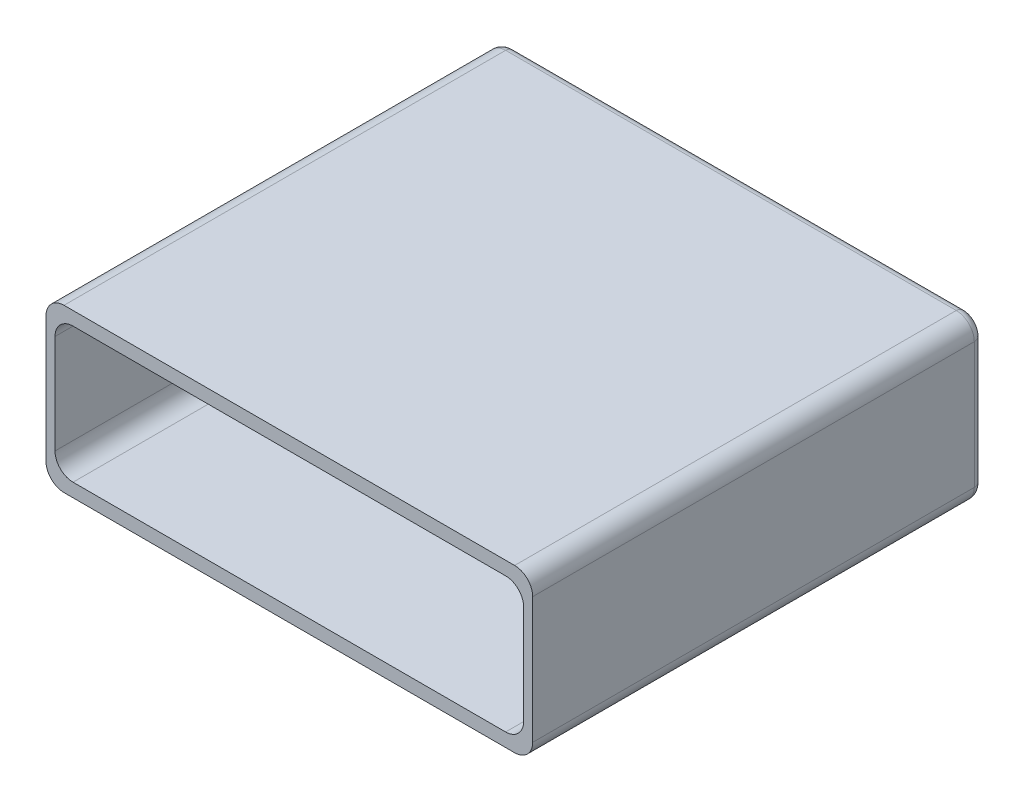
SolidWorks part; units mm, degrees
ref_plane "Front Plane" through (0, 0, 0) normal (0, 0, 1) x (1, 0, 0)
ref_plane "Top Plane" through (0, 0, 0) normal (0, 1, 0) x (1, 0, 0)
ref_plane "Right Plane" through (0, 0, 0) normal (1, 0, 0) x (0, 0, -1)
sketch "Sketch1" plane through (0, 0, 0) normal (0, 0, 1) x (1, 0, 0)
  line L9 (25, 9) -> (-25, 9)
  line L10 (27, 7) -> (27, -7)
  line L11 (25, -9) -> (-25, -9)
  line L12 (-27, 7) -> (-27, -7)
  arc A0 (-27, -7) -> (-25, -9) centre (-25, -7) ccw
  arc A1 (27, -7) -> (25, -9) centre (25, -7) cw
  arc A2 (25, 9) -> (27, 7) centre (25, 7) cw
  arc A3 (-25, 9) -> (-27, 7) centre (-25, 7) ccw
  dimension "D1" = 2
extrude "Boss-Extrude1" add sketch "Sketch1" along normal blind 50
sketch "Sketch2" plane through (0, 0, 50) normal (0, 0, 1) x (1, 0, 0)
  line L1 (24, -7.5) -> (-24, -7.5)
  line L2 (26, -5.5) -> (26, 5.5)
  line L3 (24, 7.5) -> (-24, 7.5)
  line L4 (-26, -5.5) -> (-26, 5.5)
  line L5 (26, -7.5) -> (-26, 7.5) construction
  line L6 (26, 7.5) -> (-26, -7.5) construction
  arc A0 (24, -7.5) -> (26, -5.5) centre (24, -5.5) ccw
  arc A1 (26, 5.5) -> (24, 7.5) centre (24, 5.5) ccw
  arc A2 (-24, 7.5) -> (-26, 5.5) centre (-24, 5.5) ccw
  arc A3 (-26, -5.5) -> (-24, -7.5) centre (-24, -5.5) ccw
  point P0 (0, 0)
  dimension "D1" = 2
extrude "Cut-Extrude1" cut sketch "Sketch2" against normal blind 48
fillet "Fillet1" radius 1 8 edges at (-26.4142, -8.4142, 0) (-27, 0, 0) (-26.4142, 8.4142, 0) (0, 9, 0) (26.4142, 8.4142, 0) (27, 0, 0) (26.4142, -8.4142, 0) (0, -9, 0)
